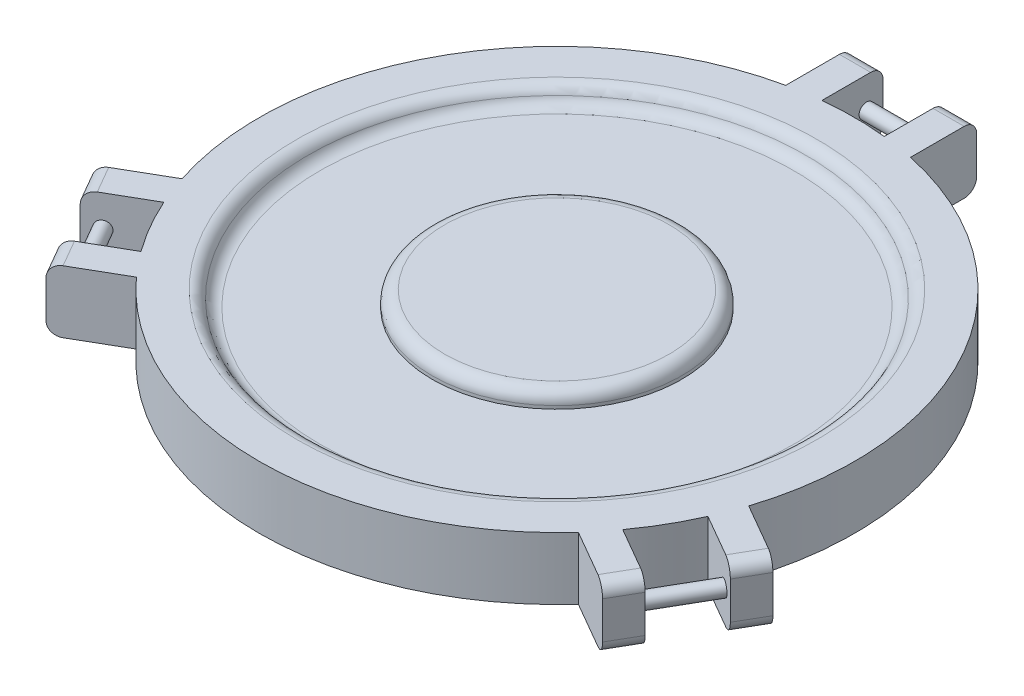
SolidWorks part; units mm, degrees
ref_plane "Front Plane" through (0, 0, 0) normal (0, 0, 1) x (1, 0, 0)
ref_plane "Top Plane" through (0, 0, 0) normal (0, 1, 0) x (1, 0, 0)
ref_plane "Right Plane" through (0, 0, 0) normal (1, 0, 0) x (0, 0, -1)
sketch "Sketch1" plane through (0, 0, 0) normal (0, 1, 0) x (1, 0, 0)
  line L0 (177.1794, -160.0296) -> (223.1172, -186.5518)
  line L1 (-25, 286.5011) -> (-50, 286.5011)
  line L2 (-50, 286.5011) -> (-50, 233.4566)
  line L4 (50, 233.4566) -> (50, 286.5011)
  line L5 (50, 286.5011) -> (25, 286.5011)
  line L6 (-25, 286.5011) -> (-25, 237.4384)
  line L7 (25, 286.5011) -> (25, 237.4384)
  line L8 (223.1172, -186.5518) -> (235.6172, -164.9012)
  line L9 (235.6172, -164.9012) -> (193.1277, -140.3698)
  line L10 (260.6172, -121.5999) -> (218.1277, -97.0686)
  line L11 (260.6172, -121.5999) -> (273.1172, -99.9493)
  line L12 (273.1172, -99.9493) -> (227.1794, -73.427)
  line L13 (-227.1794, -73.427) -> (-273.1172, -99.9493)
  line L14 (-273.1172, -99.9493) -> (-260.6172, -121.5999)
  line L15 (-260.6172, -121.5999) -> (-218.1277, -97.0686)
  line L16 (-235.6172, -164.9012) -> (-193.1277, -140.3698)
  line L17 (-235.6172, -164.9012) -> (-223.1172, -186.5518)
  line L18 (-223.1172, -186.5518) -> (-177.1794, -160.0296)
  arc A0 (25, 237.4384) -> (-25, 237.4384) centre (0, 0) ccw
  arc A1 (-50, 233.4566) -> (-227.1794, -73.427) centre (0, 0) ccw
  arc A2 (-218.1277, -97.0686) -> (-193.1277, -140.3698) centre (0, 0) ccw
  arc A3 (-177.1794, -160.0296) -> (177.1794, -160.0296) centre (0, 0) ccw
  arc A4 (193.1277, -140.3698) -> (218.1277, -97.0686) centre (0, 0) ccw
  arc A5 (227.1794, -73.427) -> (50, 233.4566) centre (0, 0) ccw
  point P29 (0, 0)
  dimension "D1" = 3
extrude "Boss-Extrude1" add sketch "Sketch1" along normal blind 50
sketch "Sketch2" plane through (0, 50, 0) normal (0, 1, 0) x (1, 0, 0)
  circle A0 centre (0, 0) radius 200
extrude "Cut-Extrude1" cut sketch "Sketch2" against normal blind 12.5
sketch "Sketch3" plane through (0, 37.5, 0) normal (0, 1, 0) x (1, 0, 0)
  circle A0 centre (0, 0) radius 100
extrude "Boss-Extrude2" add sketch "Sketch3" along normal blind 12.5
fillet "Fillet1" radius 10 12 edges at (37.5, 0, -286.5011) (-37.5, 0, -286.5011) (-37.5, 50, -286.5011) (37.5, 50, -286.5011) (229.3672, 0, 175.7265) (266.8672, 0, 110.7746) (266.8672, 50, 110.7746) (229.3672, 50, 175.7265) (-266.8672, 0, 110.7746) (-229.3672, 0, 175.7265) (-229.3672, 50, 175.7265) (-266.8672, 50, 110.7746)
fillet "Fillet8" radius 10 1 edges at (0, 50, 100)
fillet "Fillet10" radius 10 1 edges at (0, 37.5, 200)
fillet "Fillet11" radius 10 1 edges at (0, 50, 200)
sketch "Sketch4" plane through (0, 0, 0) normal (1, 0, 0) x (0, 0, -1)
  line L0 (233.4566, 50) -> (286.5011, 50) construction
  line L1 (286.5011, 50) -> (286.5011, 0) construction
  line L2 (288.8886, 0) -> (-288.8886, 0) construction
  line L3 (286.5011, 0) -> (276.5011, 0) construction
  line L4 (233.4566, 0) -> (276.5011, 0)
  line L5 (286.5011, 10) -> (286.5011, 40)
  line L6 (276.5011, 50) -> (233.4566, 50)
  line L7 (233.4566, 50) -> (233.4566, 0)
  line L8 (233.4566, 0) -> (276.5011, 0) construction
  line L9 (286.5011, 10) -> (286.5011, 40) construction
  line L10 (276.5011, 50) -> (233.4566, 50) construction
  line L11 (233.4566, 50) -> (233.4566, 0) construction
  line L12 (259.9789, 50) -> (259.9789, 0) construction
  line L13 (259.9789, 0) -> (286.5011, 50) construction
  line L14 (286.5011, 50) -> (259.9789, 50) construction
  line L15 (259.9789, 50) -> (286.5011, 0) construction
  circle A0 centre (273.24, 25) radius 6
  arc A2 (276.5011, 0) -> (286.5011, 10) centre (276.5011, 10) ccw
  arc A3 (286.5011, 40) -> (276.5011, 50) centre (276.5011, 40) ccw
  arc A4 (276.5011, 0) -> (286.5011, 10) centre (276.5011, 10) ccw construction
  arc A5 (286.5011, 40) -> (276.5011, 50) centre (276.5011, 40) ccw construction
  dimension "D2" = 12
  dimension "D1" = 0
extrude "Boss-Extrude3" add sketch "Sketch4" along normal blind 36 and the other way blind 36
pattern_circular "CirPattern1" count 3 over 360 about axis through (0, 50, 0) along (0, -1, 0) of "Boss-Extrude3"
